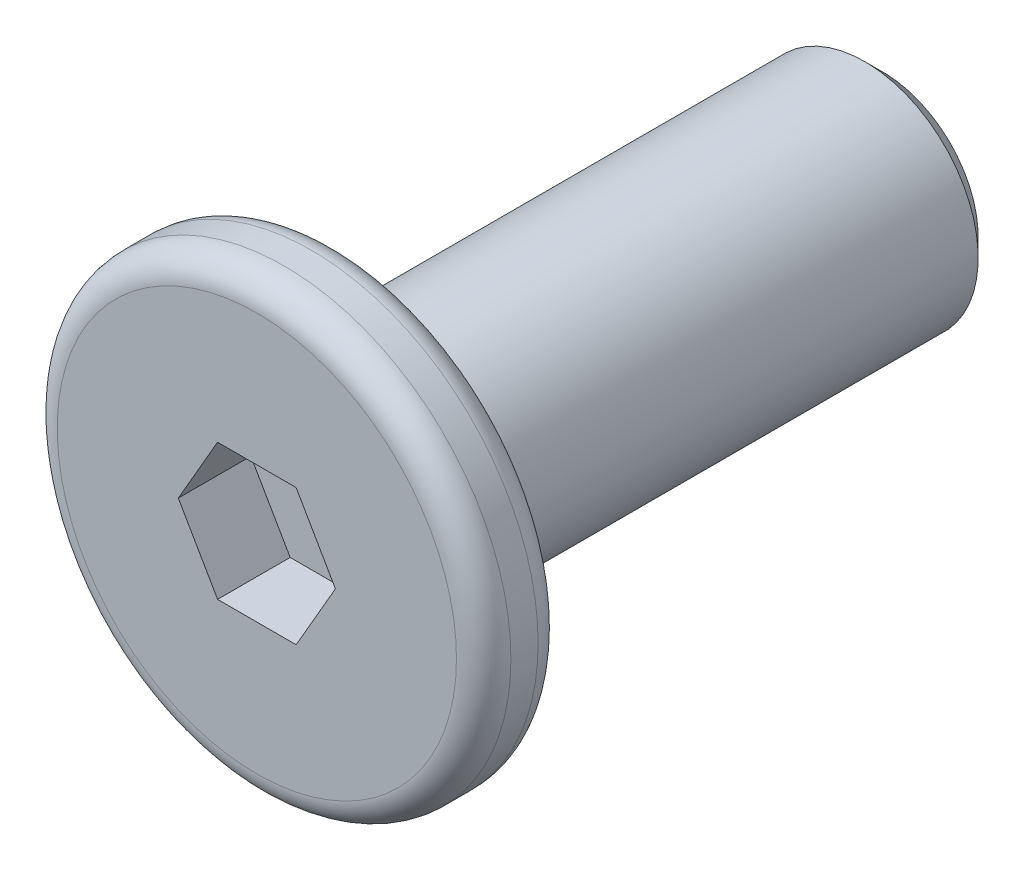
SolidWorks part; units mm, degrees
ref_plane "前视基准面" through (0, 0, 0) normal (0, 0, 1) x (1, 0, 0)
ref_plane "上视基准面" through (0, 0, 0) normal (0, 1, 0) x (1, 0, 0)
ref_plane "右视基准面" through (0, 0, 0) normal (1, 0, 0) x (0, 0, -1)
sketch "草图1" plane through (0, 0, 0) normal (0, 0, 1) x (1, 0, 0)
  circle A0 centre (0, 0) radius 2.5
  dimension "D1" = 5
extrude "凸台-拉伸1" add sketch "草图1" along normal mid plane 0.9
sketch "草图2" plane through (0, 0, -0.45) normal (0, 0, -1) x (-1, 0, 0)
  circle A0 centre (0, 0) radius 1.25
  dimension "D1" = 2.5
extrude "凸台-拉伸2" add sketch "草图2" along normal blind 6
chamfer "倒角1" distance 0.2 angle 45 1 edges at (-1.25, 0, -6.45)
sketch "草图3" plane through (0, 0, 0.45) normal (0, 0, 1) x (1, 0, 0)
  line L1 (0.866, 0) -> (0.433, 0.75)
  line L2 (0.433, 0.75) -> (-0.433, 0.75)
  line L3 (-0.433, 0.75) -> (-0.866, 0)
  line L4 (-0.866, 0) -> (-0.433, -0.75)
  line L5 (-0.433, -0.75) -> (0.433, -0.75)
  line L6 (0.433, -0.75) -> (0.866, 0)
  circle A0 centre (0, 0) radius 0.75 construction
  dimension "D1" = 1.5
extrude "切除-拉伸1" cut sketch "草图3" against normal blind 0.8
fillet "圆角2" radius 0.3 2 edges at (2.5, 0, -0.45) (2.5, 0, 0.45)
